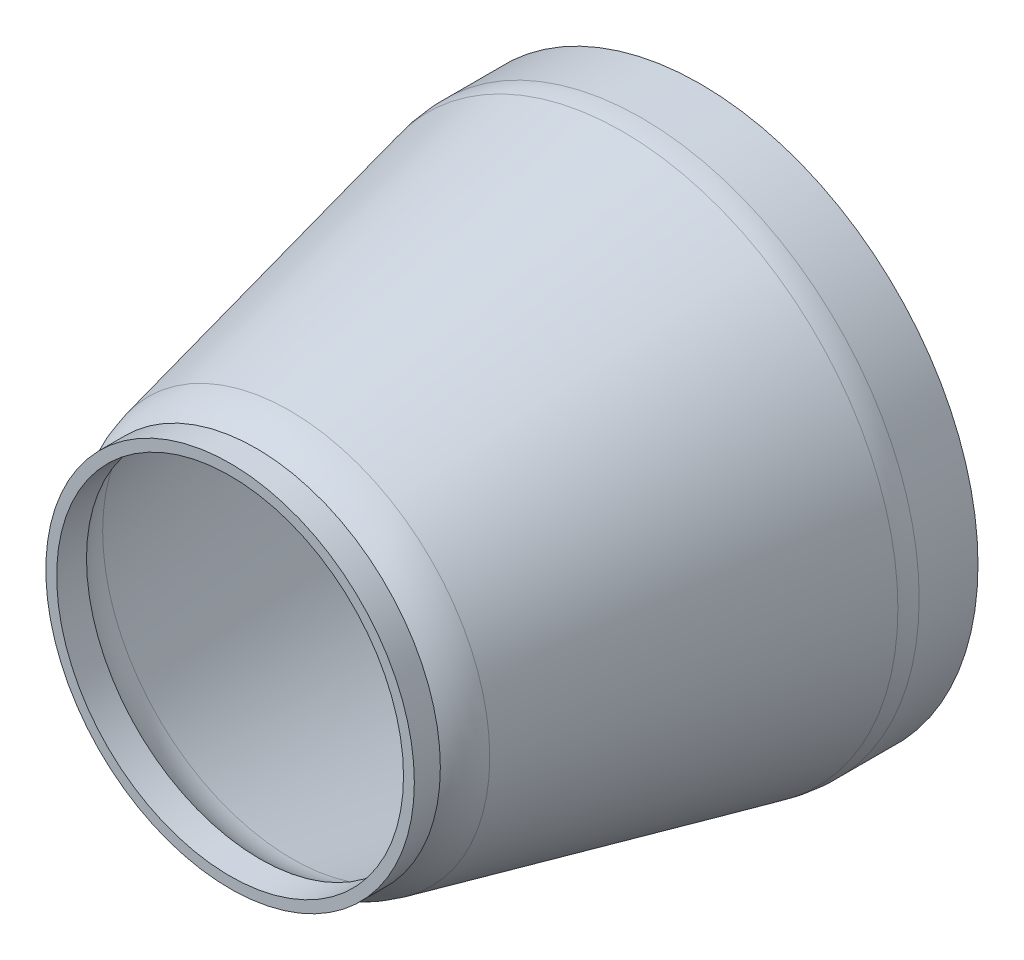
SolidWorks part; units mm, degrees
ref_plane "Front Plane" through (0, 0, 0) normal (0, 0, 1) x (1, 0, 0)
ref_plane "Top Plane" through (0, 0, 0) normal (0, 1, 0) x (1, 0, 0)
ref_plane "Right Plane" through (0, 0, 0) normal (1, 0, 0) x (0, 0, -1)
sketch "Sketch2" plane through (0, 0, 0) normal (0, 1, 0) x (1, 0, 0)
  line L0 (0, -108.5) -> (0, -6)
  line L1 (0, -6) -> (47.8162, -6)
  line L2 (47.8162, -6) -> (50, 0)
  line L3 (50, 0) -> (64, 0)
  line L4 (64, 0) -> (64, -15.8)
  line L5 (64, -15.8) -> (46.1372, -94.742)
  line L7 (42.5, -108.5) -> (0, -108.5)
  line L8 (42.5, -108.5) -> (42.5, -102.5)
  arc A0 (46.1372, -94.742) -> (42.5, -102.5) centre (26.6304, -90.3281) cw
  dimension "D8" = 20
  dimension "D1" = 108.5
  dimension "D2" = 64
  dimension "D3" = 6
  dimension "D4" = 110
  dimension "D5" = 14
  dimension "D6" = 6
  dimension "D7" = 42.5
  dimension "D9" = 167.25
  dimension "D10" = 15.8
revolve "Revolve1" add sketch "Sketch2" angle 360 about L0
fillet "Fillet1" radius 20 1 edges at (64, 0, 15.8)
shell "Shell1" thickness 2.5
